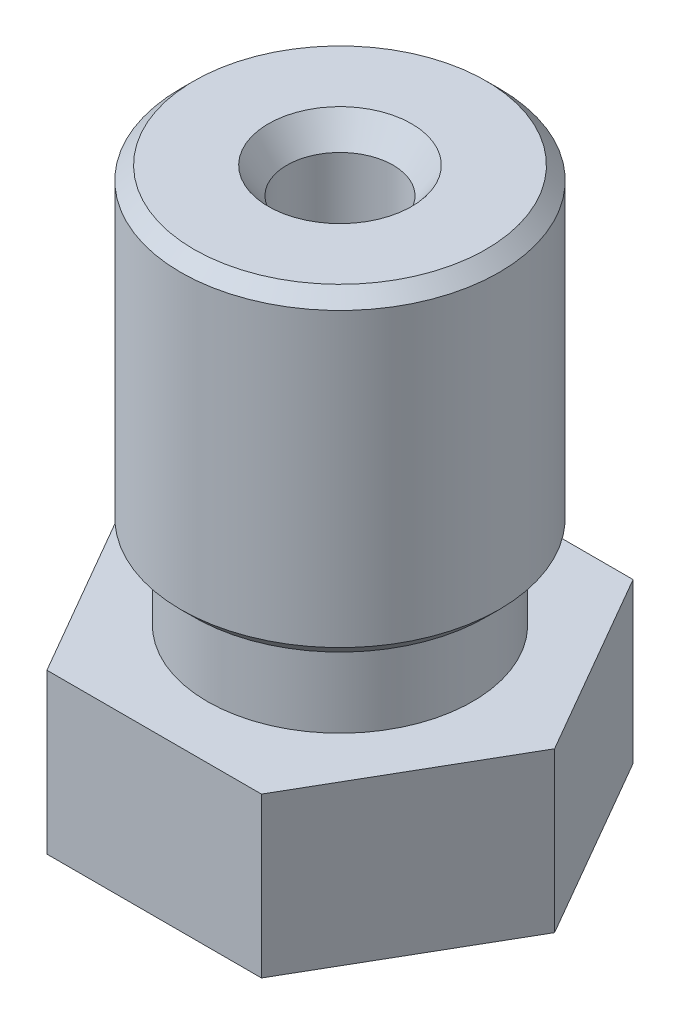
SolidWorks part; units mm, degrees
material "Brass"
ref_plane "Front Plane" through (0, 0, 0) normal (0, 0, 1) x (1, 0, 0)
ref_plane "Top Plane" through (0, 0, 0) normal (0, 1, 0) x (1, 0, 0)
ref_plane "Right Plane" through (0, 0, 0) normal (1, 0, 0) x (0, 0, -1)
sketch "Sketch1" plane through (0, 0, 0) normal (0, 0, 1) x (1, 0, 0)
  line L0 (0, -6.25) -> (0, 6.25) construction
  line L1 (0.2, -6.25) -> (0.2, -5.45)
  line L2 (0.2, -5.45) -> (0.75, -5.2051)
  line L3 (0.75, -5.2051) -> (0.75, -4.3613)
  line L4 (0.75, -4.3613) -> (1, -4.25)
  line L5 (1, -4.25) -> (1, 5.75)
  line L6 (1, 5.75) -> (1.3501, 6.25)
  line L7 (1.3501, 6.25) -> (3, 6.25)
  line L8 (2.5, 0.25) -> (3, 0.25)
  line L9 (3, 6.25) -> (3, 0.25)
  line L11 (2.5, 0.25) -> (2.5, -1.25)
  line L12 (2.5, -1.25) -> (3.5, -1.25)
  line L13 (3.5, -1.25) -> (3.5, -4.25)
  line L14 (3.5, -4.25) -> (1.9004, -4.25)
  line L15 (1.9004, -4.25) -> (0.5, -6.25)
  line L16 (0.5, -6.25) -> (0.2, -6.25)
  dimension "D1" = 12.5
  dimension "D2" = 125
  dimension "A" = 0.4
  dimension "D4" = 2
  dimension "D5" = 7
  dimension "D" = 1.5
  dimension "D6" = 6
  dimension "D7" = 125
  dimension "D8" = 0.5
  dimension "C" = 0.8
  dimension "B" = 1
  dimension "D11" = 7.5
  dimension "E" = 10.5
  dimension "D13" = 114
  dimension "D14" = 6
  dimension "D15" = 5
revolve "Revolve1" add sketch "Sketch1" angle 360 about L0
sketch "Sketch2" plane through (0, -4.25, 0) normal (0, -1, 0) x (1, 0, 0)
  line L1 (2.0207, 3.5) -> (-2.0207, 3.5)
  line L2 (-2.0207, 3.5) -> (-4.0415, 0)
  line L3 (-4.0415, 0) -> (-2.0207, -3.5)
  line L4 (-2.0207, -3.5) -> (2.0207, -3.5)
  line L5 (2.0207, -3.5) -> (4.0415, 0)
  line L6 (4.0415, 0) -> (2.0207, 3.5)
  circle A0 centre (0, 0) radius 3.5 construction
  circle A1 centre (0, 0) radius 1.6225
  dimension "D1" = 7
extrude "Boss-Extrude1" add sketch "Sketch2" against normal up to surface (3 mm away) up to face at (0, -1.25, -2.5)
chamfer "Chamfer1" distance 0.25 angle 45 2 edges at (0, 0.25, -3) (0, 6.25, -3)
